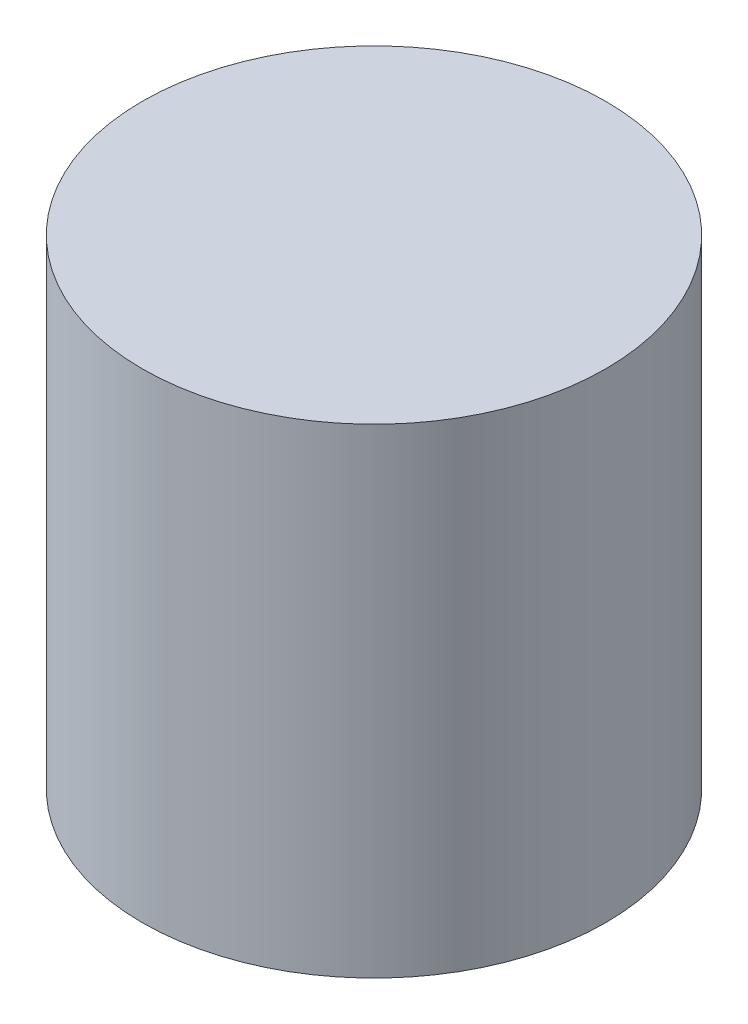
SolidWorks part; units mm, degrees
ref_plane "Front Plane" through (0, 0, 0) normal (0, 0, 1) x (1, 0, 0)
ref_plane "Top Plane" through (0, 0, 0) normal (0, 1, 0) x (1, 0, 0)
ref_plane "Right Plane" through (0, 0, 0) normal (1, 0, 0) x (0, 0, -1)
sketch "Sketch1" plane through (0, 0, 0) normal (0, 1, 0) x (1, 0, 0)
  circle A0 centre (-15.3208, 23.227) radius 11
extrude "Boss-Extrude1" add sketch "Sketch1" along normal blind 22.77
